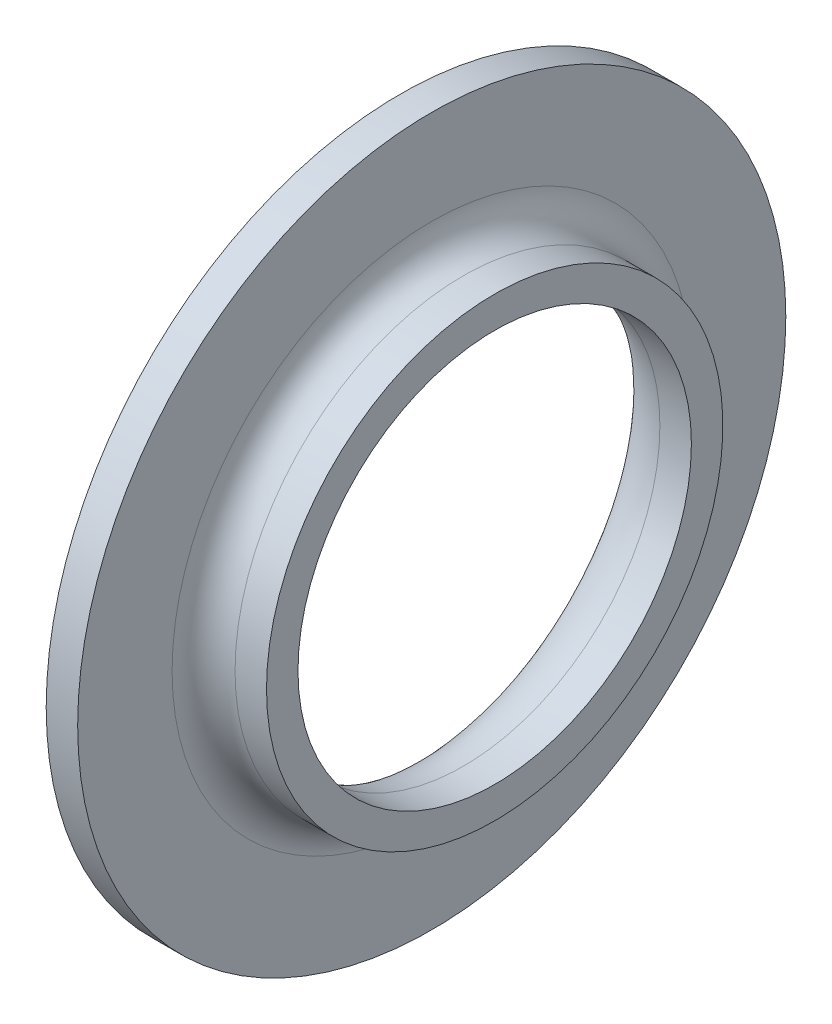
SolidWorks part; units mm, degrees
material "AISI 1020"
ref_plane "Front Plane" through (0, 0, 0) normal (0, 0, 1) x (1, 0, 0)
ref_plane "Top Plane" through (0, 0, 0) normal (0, 1, 0) x (1, 0, 0)
ref_plane "Right Plane" through (0, 0, 0) normal (1, 0, 0) x (0, 0, -1)
sketch "Sketch1" plane through (0, 0, 0) normal (0, 0, 1) x (1, 0, 0)
  line L0 (0, 45) -> (4, 45)
  line L1 (4, 45) -> (4, 33)
  line L2 (8, 29) -> (12, 29)
  line L3 (12, 29) -> (12, 25)
  line L4 (12, 25) -> (8, 25)
  line L5 (0, 33) -> (0, 45)
  line L6 (0, 0) -> (43.7266, 0) construction
  arc A0 (4, 33) -> (8, 29) centre (8, 33) ccw
  arc A1 (8, 25) -> (0, 33) centre (8, 33) cw
  dimension "D5" = 8
  dimension "D6" = 4
  dimension "D1" = 29
  dimension "D2" = 50
  dimension "D3" = 12
  dimension "D4" = 4
  dimension "D7" = 45
revolve "Revolve1" add sketch "Sketch1" angle 360 about L6
